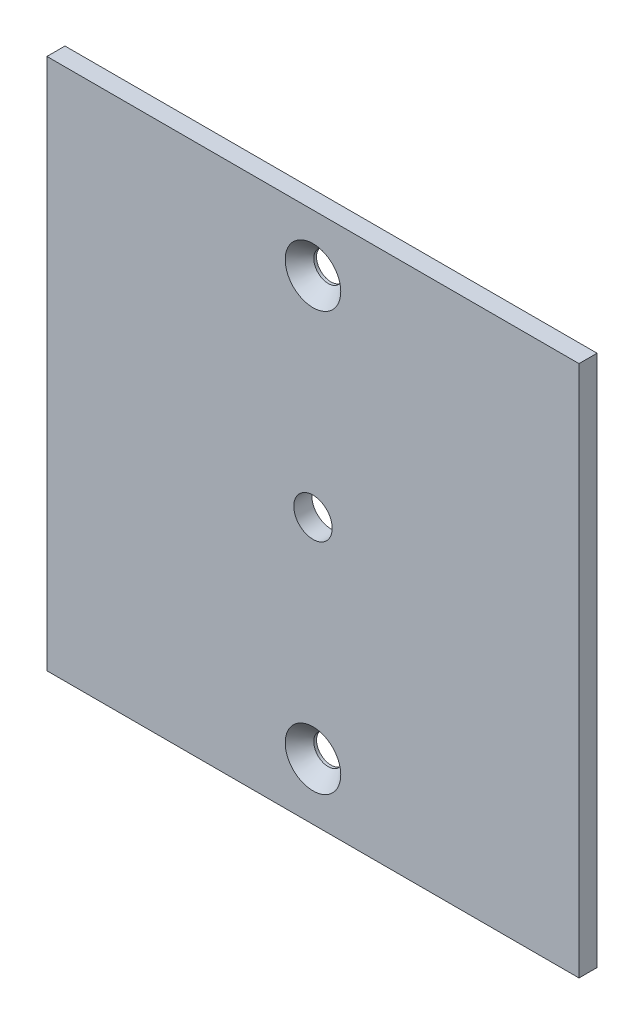
SolidWorks part; units mm, degrees
material "6061 Alloy"
ref_plane "Front Plane" through (0, 0, 0) normal (0, 0, 1) x (1, 0, 0)
ref_plane "Top Plane" through (0, 0, 0) normal (0, 1, 0) x (1, 0, 0)
ref_plane "Right Plane" through (0, 0, 0) normal (1, 0, 0) x (0, 0, -1)
sketch "Sketch1" plane through (0, 0, 0) normal (0, 0, 1) x (1, 0, 0)
  line L1 (-46.825, -46.825) -> (46.825, -46.825)
  line L2 (-46.825, -46.825) -> (-46.825, 46.825)
  line L3 (-46.825, 46.825) -> (46.825, 46.825)
  line L4 (46.825, -46.825) -> (46.825, 46.825)
  line L5 (-46.825, -46.825) -> (46.825, 46.825) construction
  line L6 (-46.825, 46.825) -> (46.825, -46.825) construction
  point P0 (0, 0)
  dimension "D1" = 93.65
  dimension "D2" = 93.65
extrude "Boss-Extrude1" add sketch "Sketch1" along normal blind 3.175
sketch "Sketch2" plane through (0, 0, 3.175) normal (0, 0, 1) x (1, 0, 0)
  point P0 (0, 0)
hole_wizard "1/4 Clearance Hole1" positions "Sketch2" profile "Sketch3" hole size "1/4" standard "ANSI Inch"
sketch "Sketch3" plane through (0, 0, 3.175) normal (1, 0, 0) x (0, -1, 0)
  line L0 (0, 0) -> (0, 6.8558)
  line L1 (0, 6.8558) -> (3.3782, 4.826)
  line L2 (3.3782, 4.826) -> (3.3782, 0)
  line L5 (3.3782, 0) -> (0, 0)
  line L10 (0, 6.8558) -> (-3.3782, 4.826) construction
  line L11 (0, -6.35) -> (0, 107.95) construction
  dimension "Hole Dia." = 6.7564
  dimension "Hole Depth" = 4.826
  dimension "Drill Angle" = 118
sketch "Sketch4" plane through (0, 0, 3.175) normal (0, 0, 1) x (1, 0, 0)
  point P0 (0, 36.825)
  point P1 (0, -36.825)
hole_wizard "CSK for #10 Flat Head Machine Screw1" positions "Sketch4" profile "Sketch5" countersink size "#10" standard "ANSI Inch"
sketch "Sketch5" plane through (0, 36.825, 3.175) normal (1, 0, 0) x (0, -1, 0)
  line L0 (0, 0) -> (0, 6.3598)
  line L1 (0, 6.3598) -> (2.5527, 4.826)
  line L2 (2.5527, 4.826) -> (2.5527, 2.6882)
  line L3 (2.5527, 2.6882) -> (4.8895, 0)
  line L5 (4.8895, 0) -> (0, 0)
  line L6 (-2.5527, 2.6882) -> (-4.8895, 0) construction
  line L10 (0, 6.3598) -> (-2.5527, 4.826) construction
  line L11 (0, -6.35) -> (0, 107.95) construction
  dimension "Hole Dia." = 5.1054
  dimension "Hole Depth" = 4.826
  dimension "Near C'Sink Dia." = 9.779
  dimension "Near C'Sink Angle" = 82
  dimension "Drill Angle" = 118
equation "\"side\"= 100mm"
equation "\"thk\"= 1 / 8"
equation "\"D1@Sketch1\"=\"side\"-(2*\"thk\")"
equation "\"D2@Sketch1\"=\"side\"-(2*\"thk\")"
equation "\"D1@Boss-Extrude1\"=\"thk\""
